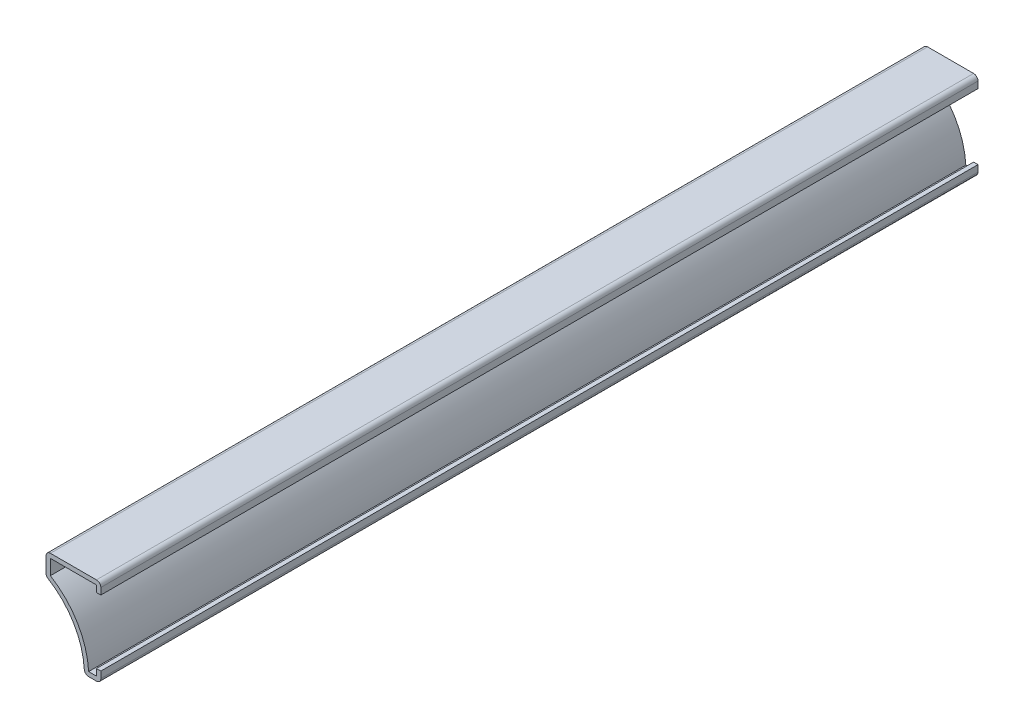
SolidWorks part; units mm, degrees
ref_plane "Front Plane" through (0, 0, 0) normal (0, 0, 1) x (1, 0, 0)
ref_plane "Top Plane" through (0, 0, 0) normal (0, 1, 0) x (1, 0, 0)
ref_plane "Right Plane" through (0, 0, 0) normal (1, 0, 0) x (0, 0, -1)
sketch "Sketch1" plane through (0, 0, 0) normal (0, 0, 1) x (1, 0, 0)
  line L0 (0, 0) -> (0, -3.175)
  line L1 (0, -3.175) -> (-4.7625, -3.175)
  line L2 (-15.875, 15.875) -> (-15.875, 22.225)
  line L3 (-15.875, 22.225) -> (0, 22.225)
  line L4 (0, 22.225) -> (0, 19.05)
  arc A0 (-4.7625, -3.175) -> (-15.875, 15.875) centre (-26.6473, -3.175) ccw
  dimension "D1" = 4.7625
  dimension "D2" = 3.175
  dimension "D3" = 3.175
  dimension "D4" = 15.875
  dimension "D5" = 6.35
  dimension "D6" = 25.4
  dimension "D7" = 19.05
extrude "Extrude-Thin1" add sketch "Sketch1" against normal blind 254 thin
fillet "Fillet1" radius 1.27 5 edges at (0, -3.175, -127) (-4.7625, -3.175, -127) (-15.875, 15.875, -127) (-15.875, 22.225, -127) (0, 22.225, -127)
